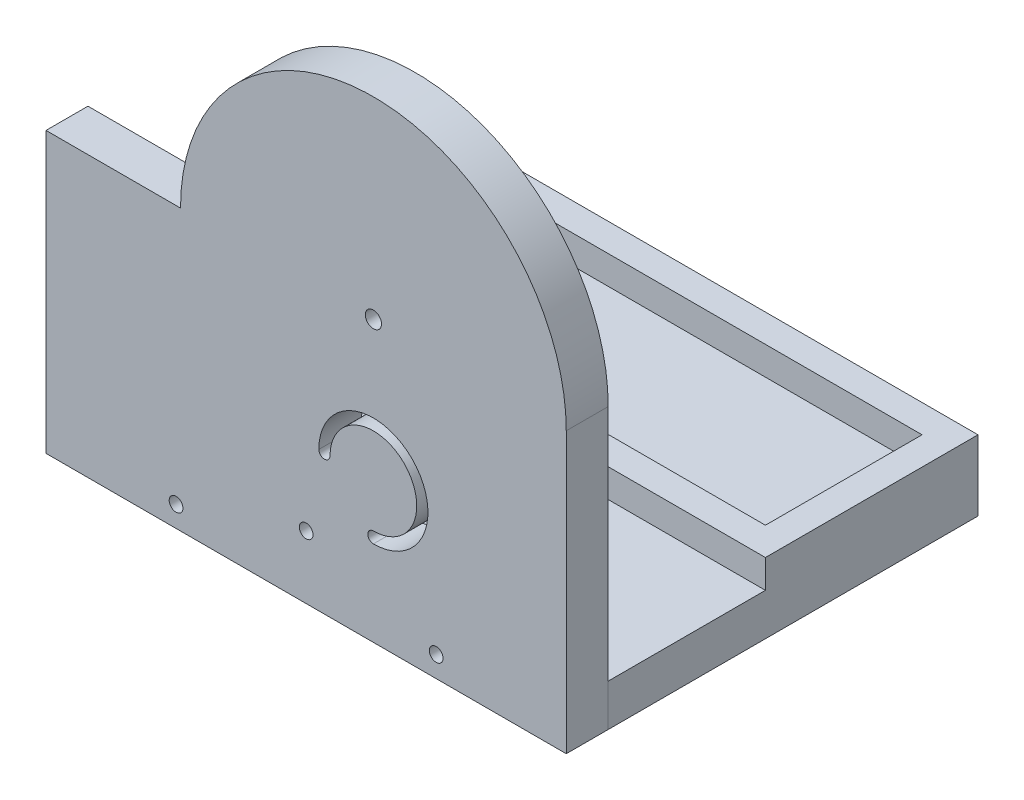
SolidWorks part; units mm, degrees
ref_plane "Front Plane" through (0, 0, 0) normal (0, 0, 1) x (1, 0, 0)
ref_plane "Top Plane" through (0, 0, 0) normal (0, 1, 0) x (1, 0, 0)
ref_plane "Right Plane" through (0, 0, 0) normal (1, 0, 0) x (0, 0, -1)
other "Center of Mass"
sketch "Sketch2" plane through (0, 0, 0) normal (1, 0, 0) x (0, 0, -1)
  line L0 (-86.852, 67.6087) -> (-86.852, -102.3913)
  line L1 (-86.852, -102.3913) -> (60.348, -102.3913)
  line L2 (60.348, -102.3913) -> (60.348, -87.3913)
  line L3 (60.348, -87.3913) -> (-71.852, -87.3913)
  line L4 (-71.852, -87.3913) -> (-71.852, 67.6087)
  line L5 (-71.852, 67.6087) -> (-86.852, 67.6087)
  dimension "D1" = 15
  dimension "D2" = 147.2
  dimension "D3" = 170
  dimension "D4" = 15
extrude "Boss-Extrude2" add sketch "Sketch2" along normal blind 186
sketch "Sketch3" plane through (0, -87.3913, 0) normal (0, 1, 0) x (1, 0, 0)
  line L0 (10, 50.348) -> (176, 50.348)
  line L1 (176, 50.348) -> (176, -5.652)
  line L2 (176, -5.652) -> (10, -5.652)
  line L3 (10, -5.652) -> (10, 50.348)
  line L4 (0, -15.652) -> (0, 60.348)
  line L5 (0, 60.348) -> (186, 60.348)
  line L6 (186, 60.348) -> (186, -15.652)
  line L7 (186, -15.652) -> (0, -15.652)
  line L8 (186, -71.852) -> (0, -71.852) construction
  line L10 (0, 60.348) -> (0, -71.852) construction
  dimension "D2" = 56.2
  dimension "D3" = 56
  dimension "D4" = 166
  dimension "D5" = 0
  dimension "D1" = 10
extrude "Boss-Extrude3" add sketch "Sketch3" along normal blind 10.16
sketch "Sketch6" plane through (0, 0, 71.852) normal (0, 0, -1) x (-1, 0, 0)
  line L0 (-157.0443, -87.3913) -> (-157.0443, 67.6087) construction
  line L1 (-186, -87.3913) -> (0, -87.3913) construction
  line L2 (-186, 67.6087) -> (0, 67.6087) construction
  line L3 (-186, -87.3913) -> (-186, 67.6087) construction
  line L4 (-117.0443, -7.3913) -> (-117.0443, -77.2313) construction
  line L5 (-186, -77.2313) -> (0, -77.2313) construction
  arc A5 (-117.0443, -69.8913) -> (-99.5443, -52.3913) centre (-117.0443, -52.3913) cw construction
  arc A6 (-97.5443, -52.3913) -> (-117.0443, -71.8913) centre (-117.0443, -52.3913) ccw
  arc A7 (-101.5443, -52.3913) -> (-117.0443, -67.8913) centre (-117.0443, -52.3913) ccw
  arc A8 (-101.5443, -52.3913) -> (-97.5443, -52.3913) centre (-99.5443, -52.3913) ccw
  arc A9 (-117.0443, -71.8913) -> (-117.0443, -67.8913) centre (-117.0443, -69.8913) ccw
  point P6 (-117.0443, -52.3913)
  point P22 (-129.4186, -40.0169)
  dimension "D4" = 0
  dimension "D5" = 17.5
  dimension "D6" = 28.9557
  dimension "D9" = 4
  dimension "D1" = 40
  dimension "D2" = 35
  dimension "D7" = 68.9557
  dimension "D8" = 0
extrude "Cut-Extrude5" cut sketch "Sketch6" against normal up to surface (15 mm away) contours A6 A9 A7 A8 up to face at (93, -17.3913, 86.852)
sketch "Sketch10" plane through (0, 0, 71.852) normal (0, 0, -1) x (-1, 0, 0)
  line L0 (-117.0443, -7.3913) -> (-117.0443, -77.2313) construction
  point P0 (-117.0443, -2.3913)
  dimension "D1" = 50
hole_wizard "M5 Clearance Hole1" positions "3DSketch1" profile "Sketch12" hole size "M5" standard "ANSI Metric" end condition through all
sketch3d "3DSketch1"
  point P0 (117.0443, -2.3913, 71.852)
sketch "Sketch12" plane through (117.0443, -2.3913, 71.852) normal (1, 0, 0) x (0, 1, 0)
  line L0 (0, 0) -> (0, 15)
  line L1 (0, 15) -> (2.9, 15)
  line L2 (2.9, 15) -> (2.9, 0)
  line L5 (2.9, 0) -> (0, 0)
  line L11 (0, -6.35) -> (0, 107.95) construction
  dimension "Thru Hole Dia." = 5.8
  dimension "Thru Hole Depth" = 15
sketch "Sketch13" plane through (0, 0, 71.852) normal (0, 0, -1) x (-1, 0, 0)
  line L0 (-48.0885, -2.3913) -> (0, -2.3913)
  line L1 (0, -87.3913) -> (0, 67.6087) construction
  line L3 (-186, -87.3913) -> (-186, 67.6087) construction
  line L4 (-186, 67.6087) -> (0, 67.6087) construction
  line L5 (0, -2.3913) -> (0, 67.6087)
  line L6 (-186, 67.6087) -> (0, 67.6087)
  line L7 (-186, -2.3913) -> (-186, 67.6087)
  arc A0 (-48.0885, -2.3913) -> (-186, -2.3913) centre (-117.0443, -2.3913) ccw
extrude "Cut-Extrude6" cut sketch "Sketch13" against normal up to surface (15 mm away) up to face at (114.1443, -2.3913, 86.852)
ref_plane "Plane2" through (0, 0, 71.852) normal (0, 0, -1) x (-1, 0, 0)
sketch "Sketch16" plane through (0, 0, 71.852) normal (0, 0, -1) x (-1, 0, 0)
  line L0 (-100.5, -79.8913) -> (-100.5, -87.3913)
  line L2 (-100.5, -87.3913) -> (-85.5, -87.3913)
  line L3 (-85.5, -87.3913) -> (-85.5, -79.8913)
  line L4 (-186, -87.3913) -> (-186, -2.3913) construction
  line L6 (-186, -87.3913) -> (0, -87.3913) construction
  arc A0 (-85.5, -79.8913) -> (-100.5, -79.8913) centre (-93, -79.8913) ccw
  dimension "D1" = 15
  dimension "D2" = 7.5
  dimension "D3" = 93
extrude "Boss-Extrude4" add sketch "Sketch16" along normal blind 15
sketch "Sketch14" plane through (0, 0, 86.852) normal (0, 0, 1) x (1, 0, 0)
  line L0 (0, -94.8913) -> (186, -94.8913) construction
  line L1 (0, -2.3913) -> (0, -102.3913) construction
  line L2 (186, -2.3913) -> (186, -102.3913) construction
  line L3 (186, -102.3913) -> (0, -102.3913) construction
  arc A0 (100.5, -79.8913) -> (85.5, -79.8913) centre (93, -79.8913) ccw construction
  point P10 (46.5, -94.8913)
  point P12 (93, -94.8913)
  point P13 (139.5, -94.8913)
  point P17 (93, -79.8913)
  dimension "D1" = 7.5
hole_wizard "#8 Clearance Hole1" positions "3DSketch2" profile "Sketch17" hole size "#8" standard "ANSI Inch"
sketch3d "3DSketch2"
  point P0 (46.5, -94.8913, 86.852)
  point P3 (93, -79.8913, 86.852)
  point P6 (139.5, -94.8913, 86.852)
sketch "Sketch17" plane through (46.5, -94.8913, 86.852) normal (1, 0, 0) x (0, -1, 0)
  line L0 (0, 0) -> (0, 31.4766)
  line L1 (0, 31.4766) -> (2.4574, 30)
  line L2 (2.4574, 30) -> (2.4574, 0)
  line L5 (2.4574, 0) -> (0, 0)
  line L10 (0, 31.4766) -> (-2.4575, 30) construction
  line L11 (0, -6.35) -> (0, 107.95) construction
  dimension "Hole Dia." = 4.9149
  dimension "Hole Depth" = 30
  dimension "Drill Angle" = 118
split "Split2" trim tools "Plane2" bodies to split 118 resulting bodies 119 120
